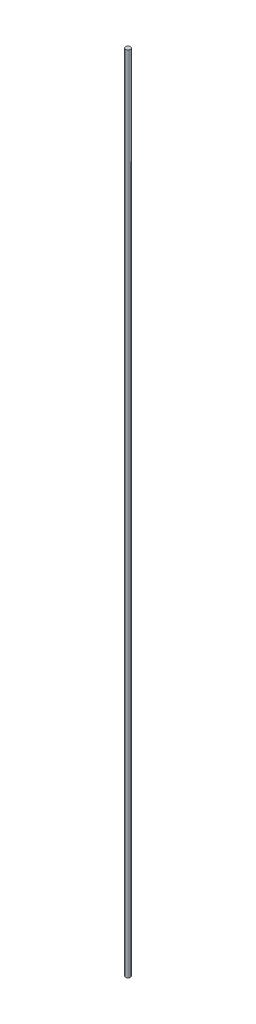
SolidWorks part; units mm, degrees
ref_plane "Front Plane" through (0, 0, 0) normal (0, 0, 1) x (1, 0, 0)
ref_plane "Top Plane" through (0, 0, 0) normal (0, 1, 0) x (1, 0, 0)
ref_plane "Right Plane" through (0, 0, 0) normal (1, 0, 0) x (0, 0, -1)
sketch "Sketch1" plane through (0, 0, 0) normal (0, 1, 0) x (1, 0, 0)
  circle A0 centre (0, 0) radius 4.7625
  dimension "D1" = 9.525
extrude "Boss-Extrude1" add sketch "Sketch1" along normal blind 1600.2
